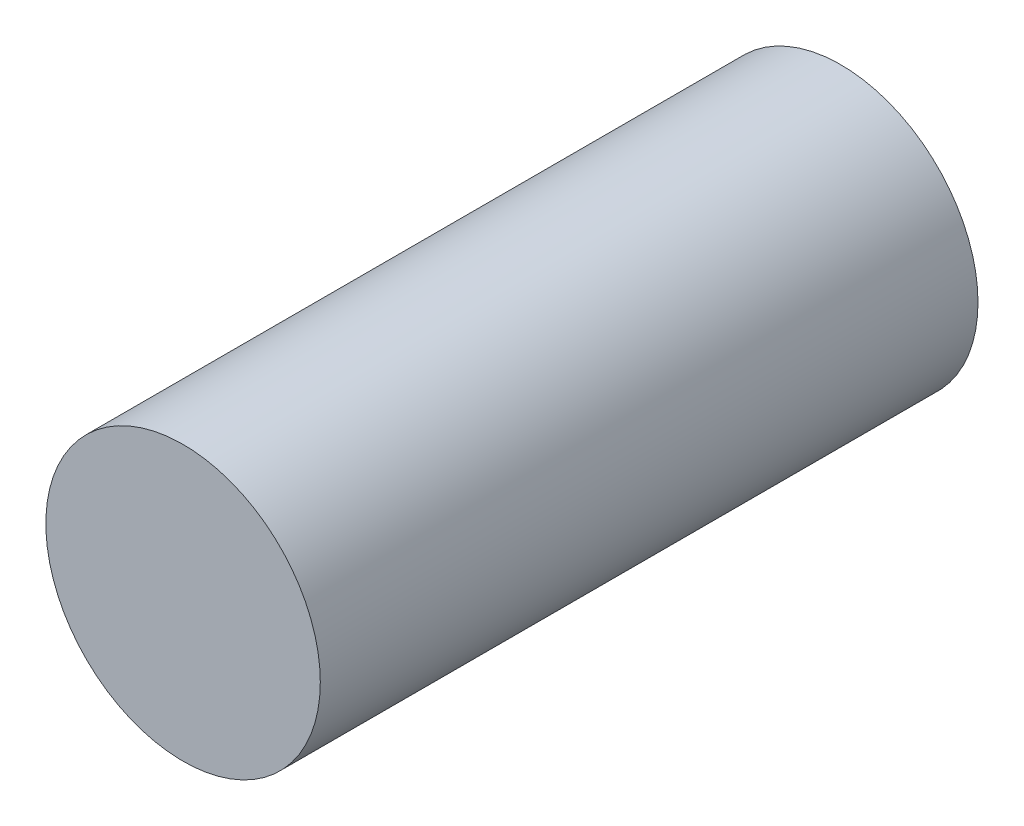
SolidWorks part; units mm, degrees
ref_plane "Front Plane" through (0, 0, 0) normal (0, 0, 1) x (1, 0, 0)
ref_plane "Top Plane" through (0, 0, 0) normal (0, 1, 0) x (1, 0, 0)
ref_plane "Right Plane" through (0, 0, 0) normal (1, 0, 0) x (0, 0, -1)
sketch "Sketch1" plane through (0, 0, 0) normal (0, 0, 1) x (1, 0, 0)
  circle A0 centre (0, 0) radius 15.9
  dimension "D1" = 31.8
extrude "Boss-Extrude1" add sketch "Sketch1" along normal blind 76.2
